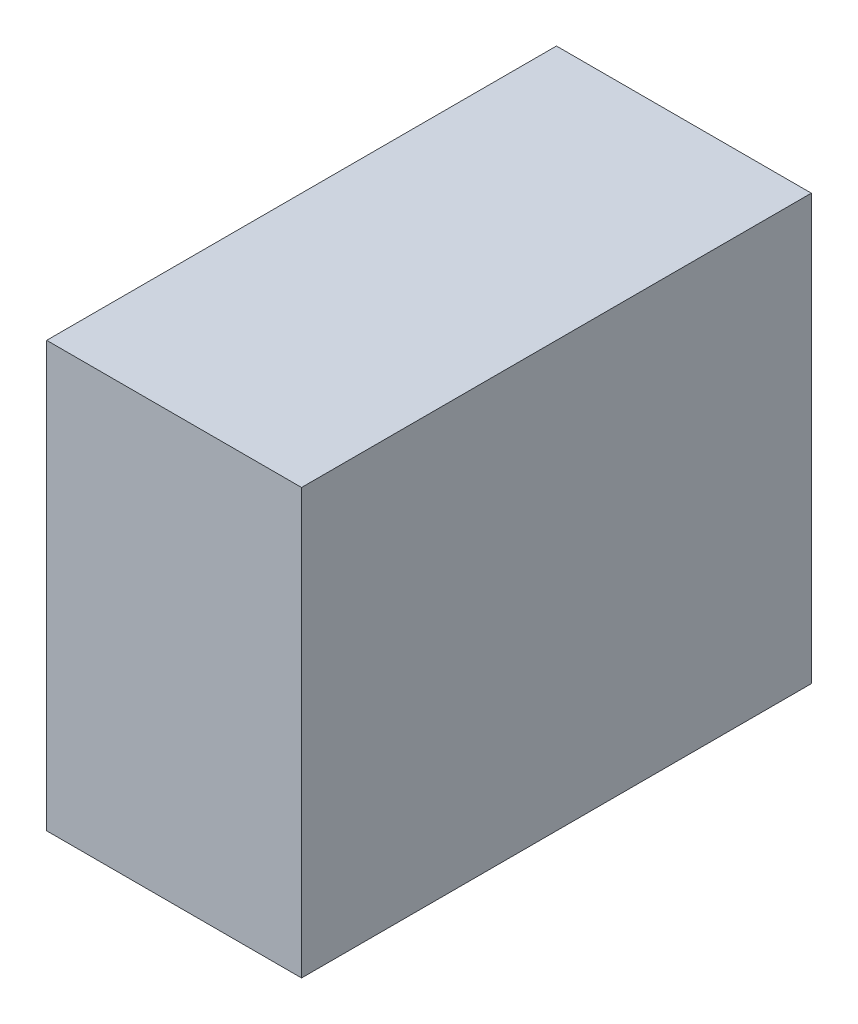
SolidWorks part; units mm, degrees
ref_plane "Front Plane" through (0, 0, 0) normal (0, 0, 1) x (1, 0, 0)
ref_plane "Top Plane" through (0, 0, 0) normal (0, 1, 0) x (1, 0, 0)
ref_plane "Right Plane" through (0, 0, 0) normal (1, 0, 0) x (0, 0, -1)
sketch "Sketch1" plane through (0, 0, 0) normal (0, 0, 1) x (1, 0, 0)
  line L1 (-19.05, -31.75) -> (19.05, -31.75)
  line L2 (-19.05, -31.75) -> (-19.05, 31.75)
  line L3 (-19.05, 31.75) -> (19.05, 31.75)
  line L4 (19.05, -31.75) -> (19.05, 31.75)
  line L5 (-19.05, -31.75) -> (19.05, 31.75) construction
  line L6 (-19.05, 31.75) -> (19.05, -31.75) construction
  point P0 (0, 0)
  dimension "D1" = 38.1
  dimension "D2" = 63.5
extrude "Boss-Extrude1" add sketch "Sketch1" along normal blind 76.2
